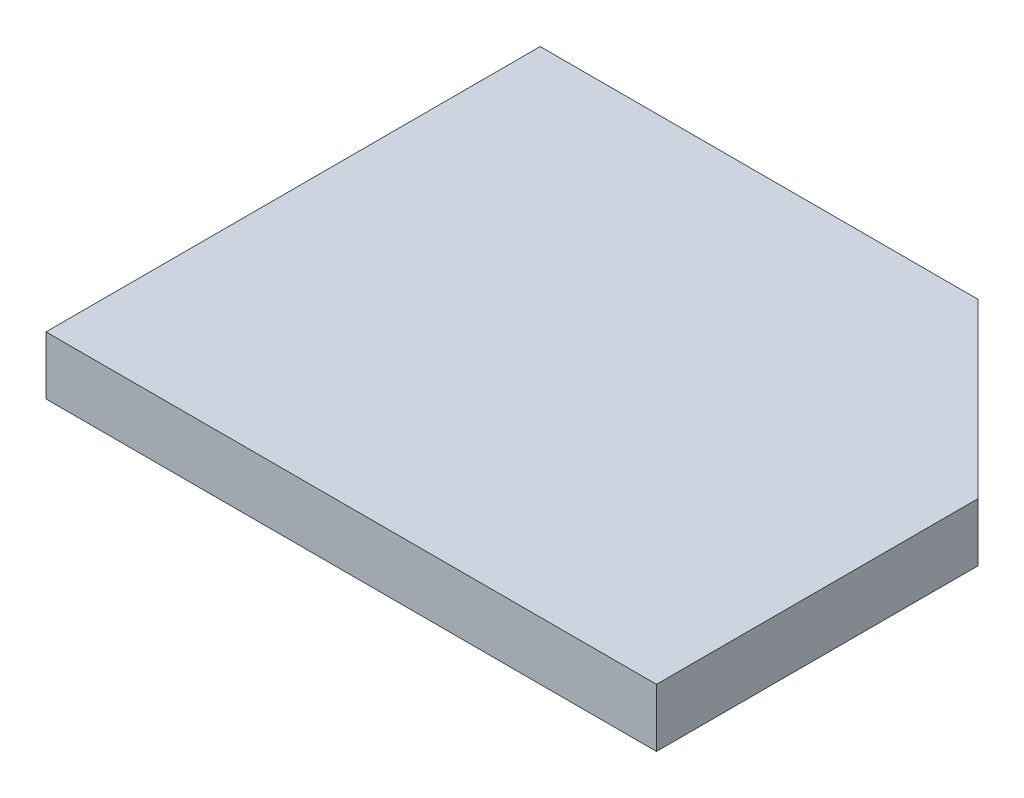
SolidWorks part; units mm, degrees
ref_plane "Front Plane" through (0, 0, 0) normal (0, 0, 1) x (1, 0, 0)
ref_plane "Top Plane" through (0, 0, 0) normal (0, 1, 0) x (1, 0, 0)
ref_plane "Right Plane" through (0, 0, 0) normal (1, 0, 0) x (0, 0, -1)
sketch "Sketch1" plane through (0, 0, 0) normal (0, 1, 0) x (1, 0, 0)
  line L0 (-41.1601, 19.7961) -> (-41.1601, -65.2039)
  line L1 (-41.1601, -65.2039) -> (63.8399, -65.2039)
  line L2 (63.8399, -65.2039) -> (63.8399, -9.9024)
  line L3 (63.8399, -9.9024) -> (34.1414, 19.7961)
  line L4 (34.1414, 19.7961) -> (-41.1601, 19.7961)
  dimension "D1" = 85
  dimension "D2" = 105
  dimension "D3" = 42
  dimension "D4" = 135
extrude "Boss-Extrude1" add sketch "Sketch1" along normal blind 10
